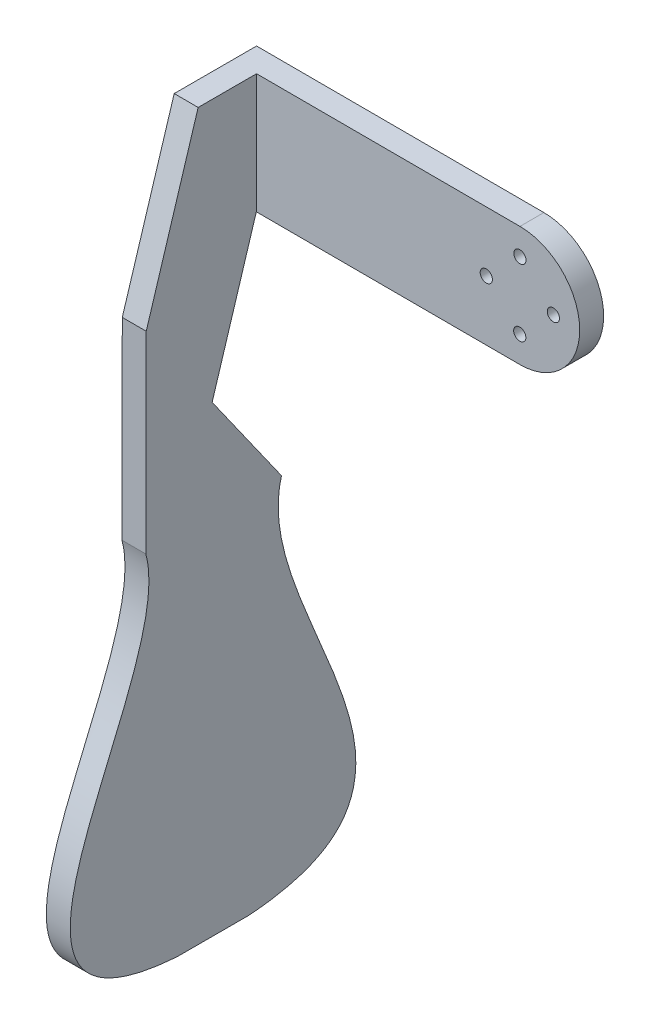
SolidWorks part; units mm, degrees
ref_plane "Front Plane" through (0, 0, 0) normal (0, 0, 1) x (1, 0, 0)
ref_plane "Top Plane" through (0, 0, 0) normal (0, 1, 0) x (1, 0, 0)
ref_plane "Right Plane" through (0, 0, 0) normal (1, 0, 0) x (0, 0, -1)
sketch "Sketch2" plane through (0, 0, 0) normal (0, 0, 1) x (1, 0, 0)
  line L0 (10, -0.0204) -> (-10, 0.0204) construction
  line L1 (-232.3607, 6.7494) -> (-131.1068, 6.5432) construction
  line L2 (-0.0204, -10) -> (0.0204, 10) construction
  circle A0 centre (0, 0) radius 10
  circle A1 centre (7, -0.0143) radius 1.275
  circle A4 centre (-0.0143, -7) radius 1.275
  circle A5 centre (0, 0) radius 10 construction
  circle A6 centre (-7, 0.0143) radius 1.275
  circle A7 centre (0.0143, 7) radius 1.275
  point P21 (0, 0)
  dimension "D1" = 2.55
  dimension "D2" = 2.55
  dimension "D3" = 7
  dimension "D4" = 7
extrude "Boss-Extrude1" add sketch "Sketch2" along normal blind 3
sketch "Sketch3" plane through (0, 0, 3) normal (0, 0, 1) x (1, 0, 0)
  line L0 (12.5, -0.0255) -> (-12.5, 0.0255) construction
  line L1 (-0.0255, -12.5) -> (0.0255, 12.5) construction
  line L3 (-0.0255, -12.5) -> (-60.0253, -12.3778)
  line L4 (0.0255, 12.5) -> (-59.9744, 12.6222)
  line L5 (-60.0253, -12.3778) -> (-59.9744, 12.6222)
  line L6 (-232.3607, 6.7494) -> (-131.1068, 6.5432) construction
  arc A0 (-0.0255, -12.5) -> (0.0255, 12.5) centre (0, 0) ccw
  circle A1 centre (7, -0.0143) radius 1.275
  circle A2 centre (-0.0143, -7) radius 1.275
  circle A3 centre (-7, 0.0143) radius 1.275
  circle A4 centre (0.0143, 7) radius 1.275
  circle A5 centre (0, 0) radius 10 construction
  point P14 (0, 0)
  dimension "D1" = 2.55
  dimension "D2" = 2.55
  dimension "D5" = 25
  dimension "D3" = 7
  dimension "D4" = 7
  dimension "D6" = 60
extrude "Boss-Extrude2" add sketch "Sketch3" against normal blind 5
sketch "Sketch4" plane through (-59.9999, 0.1222, 0) normal (-1, 0.002, 0) x (0.002, 1, 0)
  line L2 (-62.9426, -25.9706) -> (-22.6277, -25.9706)
  line L5 (12.5, -3) -> (-12.5, -3)
  line L9 (-62.9426, 2.3494) -> (-42.3963, -12.1672)
  line L10 (12.5, -3) -> (12.5, -15.1993)
  line L11 (23.5514, -11.8106) -> (-140.1922, -11.8106) construction
  line L12 (-139.2081, -4.3106) -> (-139.2081, -19.3106)
  line L13 (12.5, -15.1993) -> (-22.6277, -25.9706)
  line L14 (-12.5, -3) -> (-42.3963, -12.1672)
  line L17 (12.5, 2) -> (12.5, -3) construction
  spline S0 degree 3 poles (-62.9426, 2.3494) (-87.4923, -4.5092) (-135.6025, 45.4263) (-139.2081, -4.3106) knots 0 0 0 0 1 1 1 1
  spline S1 degree 3 poles (-62.9426, -25.9706) (-87.4923, -19.1119) (-135.6025, -69.0474) (-139.2081, -19.3106) knots 0 0 0 0 1 1 1 1
  point P8 (-91.4881, 8.073)
  point P11 (-128.2902, 17.123)
  point P17 (-153.1136, -12.427)
  dimension "D1" = 18.9923
  dimension "D2" = 25.1572
  dimension "D3" = 31.2702
extrude "Boss-Extrude3" add sketch "Sketch4" against normal blind 5
